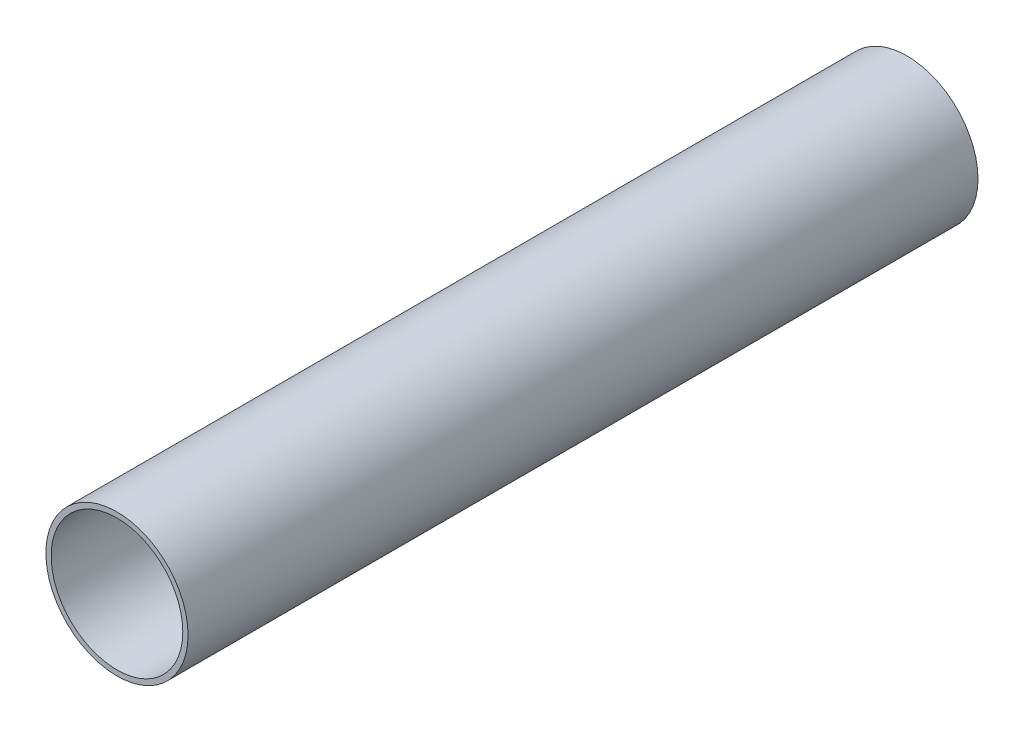
SolidWorks part; units mm, degrees
ref_plane "Front Plane" through (0, 0, 0) normal (0, 0, 1) x (1, 0, 0)
ref_plane "Top Plane" through (0, 0, 0) normal (0, 1, 0) x (1, 0, 0)
ref_plane "Right Plane" through (0, 0, 0) normal (1, 0, 0) x (0, 0, -1)
sketch "Sketch1" plane through (0, 0, 0) normal (0, 0, 1) x (1, 0, 0)
  circle A0 centre (0, 0) radius 27.432
  dimension "D1" = 54.864
extrude "Boss-Extrude1" add sketch "Sketch1" along normal mid plane 304.8
sketch "Sketch2" plane through (0, 0, 152.4) normal (0, 0, 1) x (1, 0, 0)
  circle A0 centre (0, 0) radius 25.4
  dimension "D1" = 50.8
extrude "Cut-Extrude1" cut sketch "Sketch2" against normal through all
equation "\"D1@Sketch1\" = \"diameter\"+\"pvc\""
equation "\"diameter\"=\"2\""
equation "\"pvc\"=\"0.16\""
equation "\"D1@Sketch2\" = \"diameter\""
